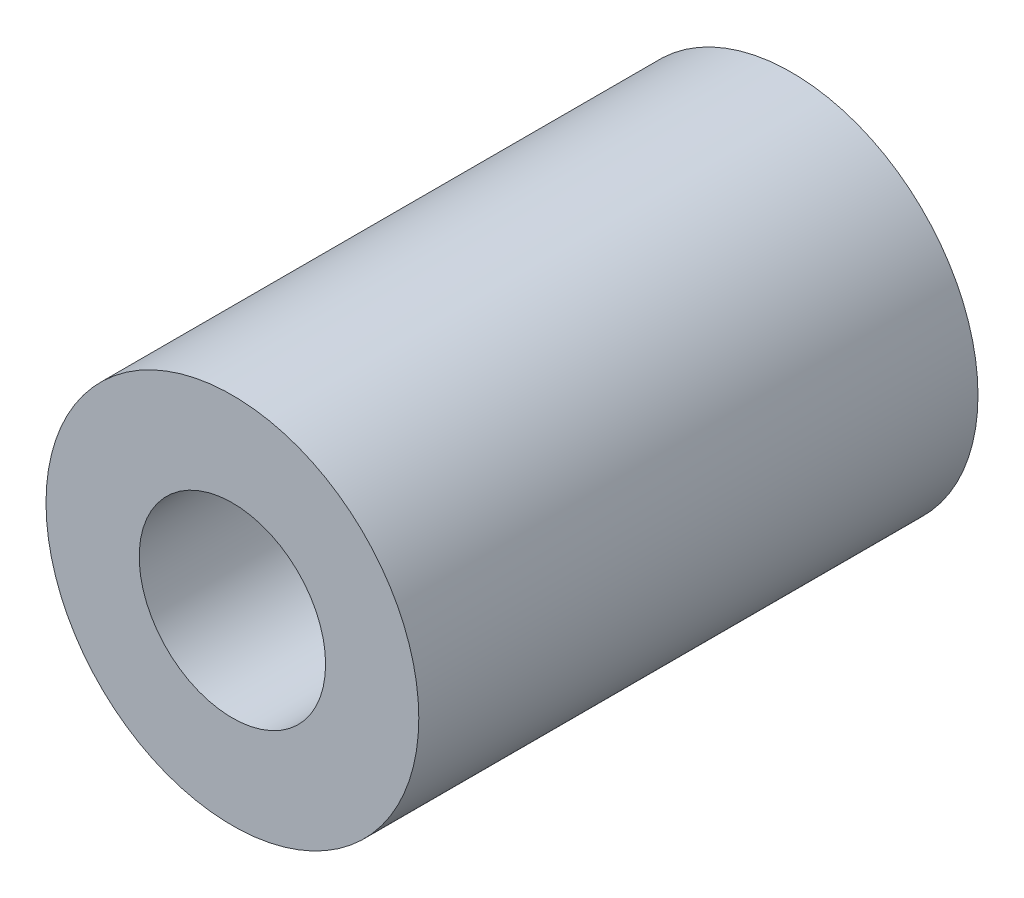
SolidWorks part; units mm, degrees
ref_plane "Plan de face" through (0, 0, 0) normal (0, 0, 1) x (1, 0, 0)
ref_plane "Plan de dessus" through (0, 0, 0) normal (0, 1, 0) x (1, 0, 0)
ref_plane "Plan de droite" through (0, 0, 0) normal (1, 0, 0) x (0, 0, -1)
sketch "Esquisse1" plane through (0, 0, 0) normal (0, 0, 1) x (1, 0, 0)
  circle A0 centre (0, 0) radius 1
  circle A1 centre (0, 0) radius 2
  dimension "D1" = 4
  dimension "D2" = 2
extrude "Boss.-Extru.1" add sketch "Esquisse1" along normal blind 6
